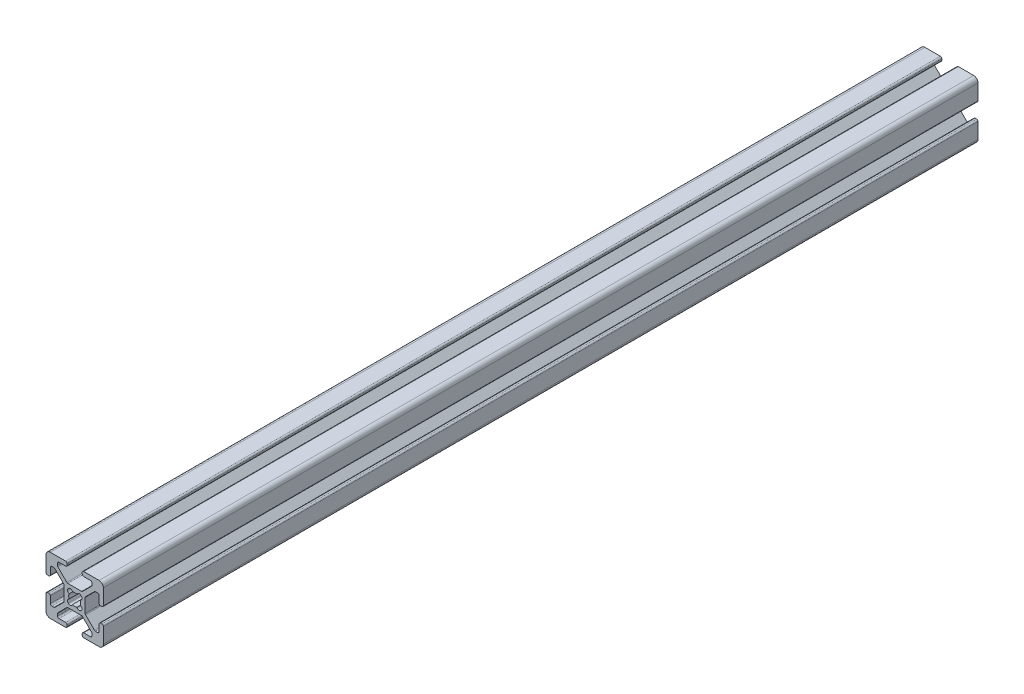
SolidWorks part; units mm, degrees
ref_plane "Front Plane" through (0, 0, 0) normal (0, 0, 1) x (1, 0, 0)
ref_plane "Top Plane" through (0, 0, 0) normal (0, 1, 0) x (1, 0, 0)
ref_plane "Right Plane" through (0, 0, 0) normal (1, 0, 0) x (0, 0, -1)
ref_plane "Plane1" through (0, 0, -457.2) normal (0, 0, -1) x (-1, 0, 0)
sketch "Sketch1" plane through (0, 0, -457.2) normal (0, 0, -1) x (-1, 0, 0)
  line L0 (2.3045, -2.1245) -> (2.1245, -2.3045)
  line L1 (-2.1245, -2.3045) -> (-2.3045, -2.1245)
  line L2 (-2.3045, 2.1245) -> (-2.1245, 2.3045)
  line L3 (2.1245, 2.3045) -> (2.3045, 2.1245)
  line L4 (10, -8.5) -> (10, -3.138)
  line L5 (9.492, -2.63) -> (9.008, -2.63)
  line L6 (8.5, -3.138) -> (8.5, -5.487)
  line L7 (7.992, -5.995) -> (7.2659, -5.995)
  line L8 (6.9067, -5.8462) -> (3.8038, -2.7433)
  line L9 (3.655, -2.3841) -> (3.655, 2.3838)
  line L10 (3.8038, 2.743) -> (6.907, 5.8462)
  line L11 (7.2662, 5.995) -> (7.992, 5.995)
  line L12 (8.5, 5.487) -> (8.5, 3.138)
  line L13 (9.008, 2.63) -> (9.492, 2.63)
  line L14 (10, 3.138) -> (10, 8.5)
  line L15 (8.5, 10) -> (3.138, 10)
  line L16 (2.63, 9.492) -> (2.63, 9.008)
  line L17 (3.138, 8.5) -> (5.487, 8.5)
  line L18 (5.995, 7.992) -> (5.995, 7.2659)
  line L19 (5.8462, 6.9067) -> (2.7433, 3.8038)
  line L20 (2.3841, 3.655) -> (-2.3838, 3.655)
  line L21 (-2.743, 3.8038) -> (-5.8462, 6.907)
  line L22 (-5.995, 7.2662) -> (-5.995, 7.992)
  line L23 (-5.487, 8.5) -> (-3.138, 8.5)
  line L24 (-2.63, 9.008) -> (-2.63, 9.492)
  line L25 (-3.138, 10) -> (-8.5, 10)
  line L26 (-10, 8.5) -> (-10, 3.138)
  line L27 (-9.492, 2.63) -> (-9.008, 2.63)
  line L28 (-8.5, 3.138) -> (-8.5, 5.487)
  line L29 (-7.992, 5.995) -> (-7.2659, 5.995)
  line L30 (-6.9067, 5.8462) -> (-3.8038, 2.7433)
  line L31 (-3.655, 2.3841) -> (-3.655, -2.3838)
  line L32 (-3.8038, -2.743) -> (-6.907, -5.8462)
  line L33 (-7.2662, -5.995) -> (-7.992, -5.995)
  line L34 (-8.5, -5.487) -> (-8.5, -3.138)
  line L35 (-9.008, -2.63) -> (-9.492, -2.63)
  line L36 (-10, -3.138) -> (-10, -8.5)
  line L37 (-8.5, -10) -> (-3.138, -10)
  line L38 (-2.63, -9.492) -> (-2.63, -9.008)
  line L39 (-3.138, -8.5) -> (-5.487, -8.5)
  line L40 (-5.995, -7.992) -> (-5.995, -7.2659)
  line L41 (-5.8462, -6.9067) -> (-2.7433, -3.8038)
  line L42 (-2.3841, -3.655) -> (2.3838, -3.655)
  line L43 (2.743, -3.8038) -> (5.8462, -6.907)
  line L44 (5.995, -7.2662) -> (5.995, -7.992)
  line L45 (5.487, -8.5) -> (3.138, -8.5)
  line L46 (2.63, -9.008) -> (2.63, -9.492)
  line L47 (3.138, -10) -> (8.5, -10)
  arc A0 (1.9358, 0.8037) -> (1.9358, -0.8037) centre (0, 0) cw
  arc A1 (1.9358, -0.8037) -> (2.3045, -2.1245) centre (1.748, -1.568) cw
  arc A2 (2.1245, -2.3045) -> (0.8037, -1.9358) centre (1.568, -1.748) cw
  arc A3 (0.8037, -1.9358) -> (-0.8037, -1.9358) centre (0, 0) cw
  arc A4 (-0.8037, -1.9358) -> (-2.1245, -2.3045) centre (-1.568, -1.748) cw
  arc A5 (-2.3045, -2.1245) -> (-1.9358, -0.8037) centre (-1.748, -1.568) cw
  arc A6 (-1.9358, -0.8037) -> (-1.9358, 0.8037) centre (0, 0) cw
  arc A7 (-1.9358, 0.8037) -> (-2.3045, 2.1245) centre (-1.748, 1.568) cw
  arc A8 (-2.1245, 2.3045) -> (-0.8037, 1.9358) centre (-1.568, 1.748) cw
  arc A9 (-0.8037, 1.9358) -> (0.8037, 1.9358) centre (0, 0) cw
  arc A10 (0.8037, 1.9358) -> (2.1245, 2.3045) centre (1.568, 1.748) cw
  arc A11 (2.3045, 2.1245) -> (1.9358, 0.8037) centre (1.748, 1.568) cw
  arc A12 (10, -3.138) -> (9.492, -2.63) centre (9.492, -3.138) ccw
  arc A13 (9.008, -2.63) -> (8.5, -3.138) centre (9.008, -3.138) ccw
  arc A14 (8.5, -5.487) -> (7.992, -5.995) centre (7.992, -5.487) cw
  arc A15 (7.2659, -5.995) -> (6.9067, -5.8462) centre (7.2659, -5.487) cw
  arc A16 (3.8038, -2.7433) -> (3.655, -2.3841) centre (4.163, -2.3841) cw
  arc A17 (3.655, 2.3838) -> (3.8038, 2.743) centre (4.163, 2.3838) cw
  arc A18 (6.907, 5.8462) -> (7.2662, 5.995) centre (7.2662, 5.487) cw
  arc A19 (7.992, 5.995) -> (8.5, 5.487) centre (7.992, 5.487) cw
  arc A20 (8.5, 3.138) -> (9.008, 2.63) centre (9.008, 3.138) ccw
  arc A21 (9.492, 2.63) -> (10, 3.138) centre (9.492, 3.138) ccw
  arc A22 (10, 8.5) -> (8.5, 10) centre (8.5, 8.5) ccw
  arc A23 (3.138, 10) -> (2.63, 9.492) centre (3.138, 9.492) ccw
  arc A24 (2.63, 9.008) -> (3.138, 8.5) centre (3.138, 9.008) ccw
  arc A25 (5.487, 8.5) -> (5.995, 7.992) centre (5.487, 7.992) cw
  arc A26 (5.995, 7.2659) -> (5.8462, 6.9067) centre (5.487, 7.2659) cw
  arc A27 (2.7433, 3.8038) -> (2.3841, 3.655) centre (2.3841, 4.163) cw
  arc A28 (-2.3838, 3.655) -> (-2.743, 3.8038) centre (-2.3838, 4.163) cw
  arc A29 (-5.8462, 6.907) -> (-5.995, 7.2662) centre (-5.487, 7.2662) cw
  arc A30 (-5.995, 7.992) -> (-5.487, 8.5) centre (-5.487, 7.992) cw
  arc A31 (-3.138, 8.5) -> (-2.63, 9.008) centre (-3.138, 9.008) ccw
  arc A32 (-2.63, 9.492) -> (-3.138, 10) centre (-3.138, 9.492) ccw
  arc A33 (-8.5, 10) -> (-10, 8.5) centre (-8.5, 8.5) ccw
  arc A34 (-10, 3.138) -> (-9.492, 2.63) centre (-9.492, 3.138) ccw
  arc A35 (-9.008, 2.63) -> (-8.5, 3.138) centre (-9.008, 3.138) ccw
  arc A36 (-8.5, 5.487) -> (-7.992, 5.995) centre (-7.992, 5.487) cw
  arc A37 (-7.2659, 5.995) -> (-6.9067, 5.8462) centre (-7.2659, 5.487) cw
  arc A38 (-3.8038, 2.7433) -> (-3.655, 2.3841) centre (-4.163, 2.3841) cw
  arc A39 (-3.655, -2.3838) -> (-3.8038, -2.743) centre (-4.163, -2.3838) cw
  arc A40 (-6.907, -5.8462) -> (-7.2662, -5.995) centre (-7.2662, -5.487) cw
  arc A41 (-7.992, -5.995) -> (-8.5, -5.487) centre (-7.992, -5.487) cw
  arc A42 (-8.5, -3.138) -> (-9.008, -2.63) centre (-9.008, -3.138) ccw
  arc A43 (-9.492, -2.63) -> (-10, -3.138) centre (-9.492, -3.138) ccw
  arc A44 (-10, -8.5) -> (-8.5, -10) centre (-8.5, -8.5) ccw
  arc A45 (-3.138, -10) -> (-2.63, -9.492) centre (-3.138, -9.492) ccw
  arc A46 (-2.63, -9.008) -> (-3.138, -8.5) centre (-3.138, -9.008) ccw
  arc A47 (-5.487, -8.5) -> (-5.995, -7.992) centre (-5.487, -7.992) cw
  arc A48 (-5.995, -7.2659) -> (-5.8462, -6.9067) centre (-5.487, -7.2659) cw
  arc A49 (-2.7433, -3.8038) -> (-2.3841, -3.655) centre (-2.3841, -4.163) cw
  arc A50 (2.3838, -3.655) -> (2.743, -3.8038) centre (2.3838, -4.163) cw
  arc A51 (5.8462, -6.907) -> (5.995, -7.2662) centre (5.487, -7.2662) cw
  arc A52 (5.995, -7.992) -> (5.487, -8.5) centre (5.487, -7.992) cw
  arc A53 (3.138, -8.5) -> (2.63, -9.008) centre (3.138, -9.008) ccw
  arc A54 (2.63, -9.492) -> (3.138, -10) centre (3.138, -9.492) ccw
  arc A55 (8.5, -10) -> (10, -8.5) centre (8.5, -8.5) ccw
extrude "Boss-Extrude1" add sketch "Sketch1" against normal blind 304.8
